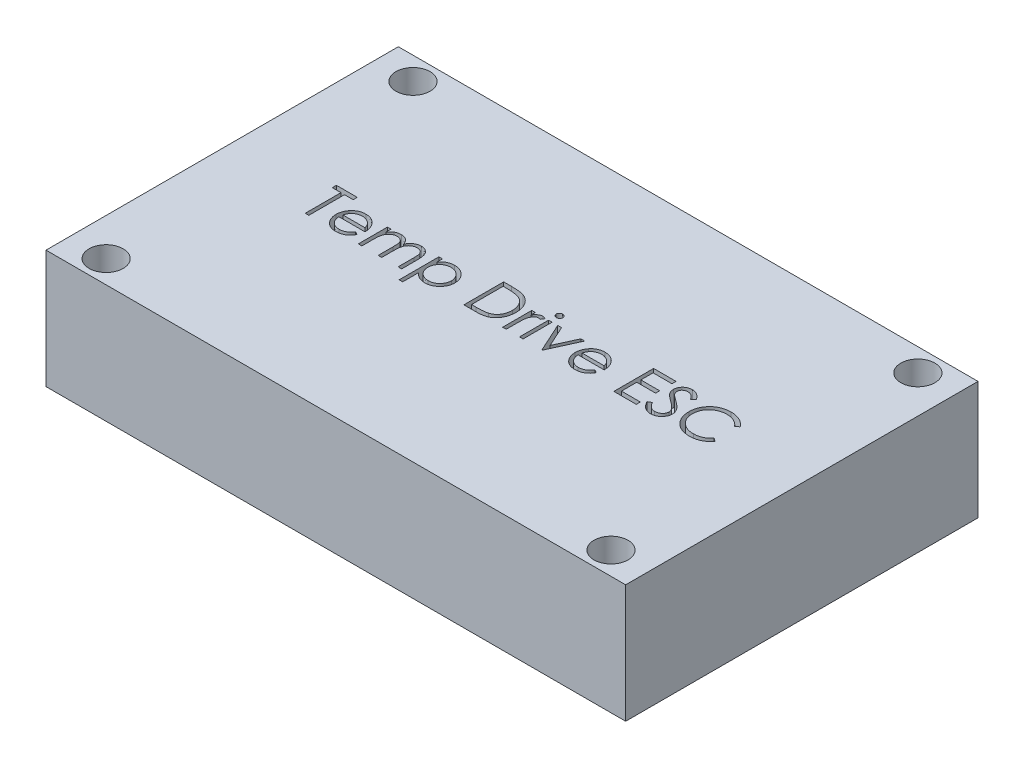
SolidWorks part; units mm, degrees
ref_plane "Front Plane" through (0, 0, 0) normal (0, 0, 1) x (1, 0, 0)
ref_plane "Top Plane" through (0, 0, 0) normal (0, 1, 0) x (1, 0, 0)
ref_plane "Right Plane" through (0, 0, 0) normal (1, 0, 0) x (0, 0, -1)
sketch "Sketch1" plane through (0, 0, 0) normal (0, 1, 0) x (1, 0, 0)
  line L0 (-22.2097, 13.5) -> (-22.2097, -13.5) construction
  line L1 (-25.5, -15.5) -> (25.5, -15.5)
  line L2 (-25.5, -15.5) -> (-25.5, 15.5)
  line L3 (-25.5, 15.5) -> (25.5, 15.5)
  line L4 (25.5, -15.5) -> (25.5, 15.5)
  line L5 (-25.5, -15.5) -> (25.5, 15.5) construction
  line L6 (-25.5, 15.5) -> (25.5, -15.5) construction
  line L7 (-22.2097, -13.5) -> (22.2097, -13.5) construction
  line L8 (22.2097, -13.5) -> (22.2097, 13.5) construction
  line L9 (22.2097, 13.5) -> (-22.2097, 13.5) construction
  circle A0 centre (-22.2097, 13.5) radius 1.5
  circle A1 centre (22.2097, 13.5) radius 1.5
  circle A2 centre (22.2097, -13.5) radius 1.5
  circle A3 centre (-22.2097, -13.5) radius 1.5
  point P0 (0, 0)
  dimension "D3" = 3
  dimension "D4" = 3
  dimension "D5" = 3
  dimension "D6" = 3
  dimension "D1" = 51
  dimension "D2" = 31
  dimension "D7" = 2
  dimension "D8" = 2
  dimension "D9" = 2
  dimension "D10" = 2
  dimension "D11" = 44.4194
  dimension "D12" = 27
extrude "Boss-Extrude1" add sketch "Sketch1" along normal blind 10.4
sketch "Sketch2" plane through (0, 10.4, 0) normal (0, 1, 0) x (1, 0, 0)
  text T0 "Temp Drive ESC"
extrude "Cut-Extrude1" cut sketch "Sketch2" against normal blind 1.4
